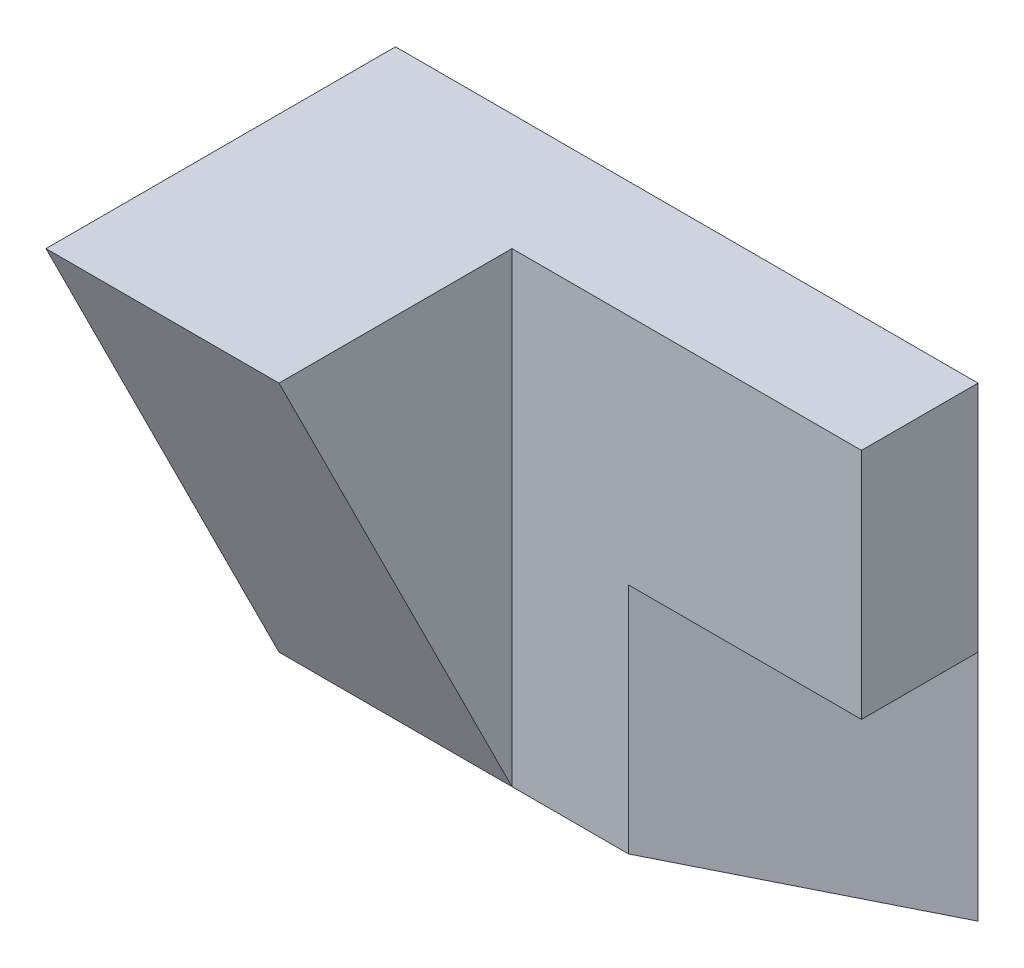
SolidWorks part; units mm, degrees
ref_plane "Front Plane" through (0, 0, 0) normal (0, 0, 1) x (1, 0, 0)
ref_plane "Top Plane" through (0, 0, 0) normal (0, 1, 0) x (1, 0, 0)
ref_plane "Right Plane" through (0, 0, 0) normal (1, 0, 0) x (0, 0, -1)
sketch "Sketch2" plane through (0, 0, 0) normal (0, 0, 1) x (1, 0, 0)
  line L1 (25, -20) -> (-25, -20)
  line L2 (25, -20) -> (25, 20)
  line L3 (25, 20) -> (-25, 20)
  line L4 (-25, -20) -> (-25, 20)
  line L5 (25, -20) -> (-25, 20) construction
  line L6 (25, 20) -> (-25, -20) construction
  point P0 (0, 0)
  dimension "D1" = 50
  dimension "D2" = 40
extrude "Boss-Extrude2" add sketch "Sketch2" along normal blind 10
sketch "Sketch4" plane through (0, -20, 0) normal (0, -1, 0) x (-1, 0, 0)
  line L0 (-5, -10) -> (-25, 0)
  line L1 (25, -10) -> (-25, -10) construction
  line L2 (-25, 0) -> (-25, -10)
  line L3 (-25, -10) -> (-5, -10)
  dimension "D1" = 20
extrude "Cut-Extrude1" cut sketch "Sketch4" against normal blind 20
sketch "Sketch5" plane through (0, 0, 10) normal (0, 0, 1) x (1, 0, 0)
  line L0 (25, 20) -> (-25, 20) construction
  line L1 (-5, -20) -> (-25, -20)
  line L2 (-5, -20) -> (-5, 20)
  line L3 (-5, 20) -> (-25, 20)
  line L4 (-25, -20) -> (-25, 20)
  line L5 (-5, -20) -> (-25, 20) construction
  line L6 (-5, 20) -> (-25, -20) construction
  line L7 (-25, 20) -> (-25, -20) construction
  point P0 (-15, 0)
  dimension "D1" = 20
  dimension "D2" = 40
extrude "Boss-Extrude3" add sketch "Sketch5" along normal blind 20
sketch "Sketch6" plane through (-5, 0, 0) normal (1, 0, 0) x (0, 0, -1)
  line L0 (-10, -20) -> (-30, -20)
  line L1 (-30, -20) -> (-10, -20) construction
  line L2 (-30, -20) -> (-30, 20) construction
  line L3 (-30, -20) -> (-30, 20)
  line L4 (-30, 20) -> (-10, -20)
extrude "Cut-Extrude2" cut sketch "Sketch6" against normal blind 20
